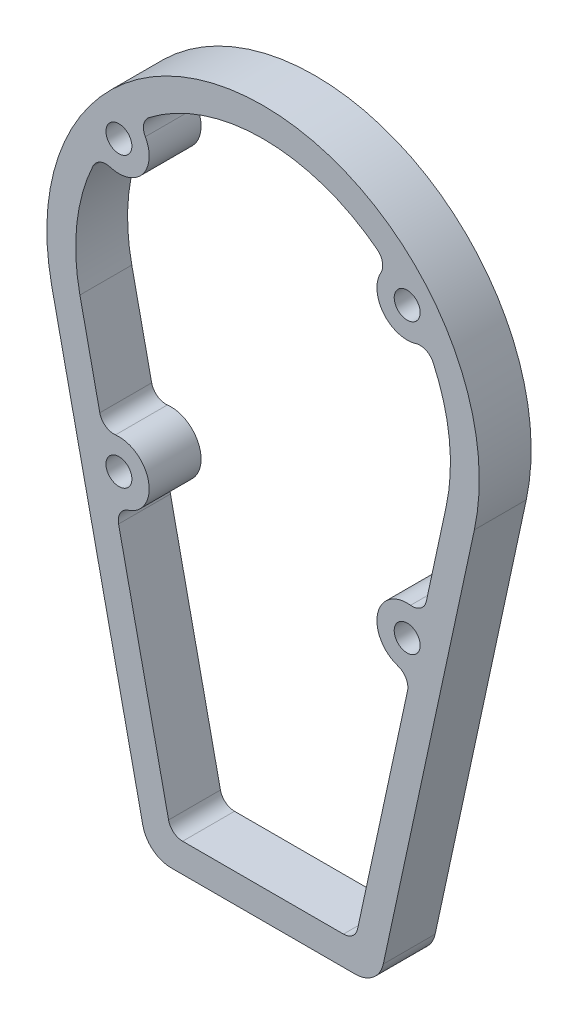
SolidWorks part; units mm, degrees
ref_plane "Front Plane" through (0, 0, 0) normal (0, 0, 1) x (1, 0, 0)
ref_plane "Top Plane" through (0, 0, 0) normal (0, 1, 0) x (1, 0, 0)
ref_plane "Right Plane" through (0, 0, 0) normal (1, 0, 0) x (0, 0, -1)
sketch "Sketch3" plane through (0, 0, 0) normal (0, 0, 1) x (1, 0, 0)
  line L0 (-31.9299, -122.5) -> (31.9299, -122.5)
  line L1 (41.7043, -114.6119) -> (73.3084, 31.6608)
  line L2 (-73.3084, 31.6608) -> (-41.7043, -114.6119)
  line L3 (-31.9299, -112.5) -> (-51.2845, -22.9211)
  line L4 (31.9299, -112.5) -> (51.2845, -22.9211)
  line L5 (-31.9299, -112.5) -> (31.9299, -112.5)
  line L6 (-55.4723, -3.5388) -> (-63.5339, 33.7727)
  line L8 (55.4723, -3.5388) -> (63.5339, 33.7727)
  arc A0 (31.9299, -122.5) -> (41.7043, -114.6119) centre (31.9299, -112.5) ccw
  arc A1 (73.3084, 31.6608) -> (-73.3084, 31.6608) centre (0, 47.5) ccw
  arc A2 (-41.7043, -114.6119) -> (-31.9299, -122.5) centre (-31.9299, -112.5) ccw
  circle A3 centre (50, -12.5) radius 4.5
  circle A4 centre (50, 87.5) radius 4.5
  circle A5 centre (-50, 87.5) radius 4.5
  circle A6 centre (-50, -12.5) radius 4.5
  arc A7 (63.5339, 33.7727) -> (56.6488, 79.3733) centre (0, 47.5) ccw
  arc A8 (-56.6488, 79.3733) -> (-43.531, 95.7706) centre (-50, 87.5) ccw
  arc A9 (43.531, 95.7706) -> (56.6488, 79.3733) centre (50, 87.5) ccw
  arc A10 (55.4723, -3.5388) -> (51.2845, -22.9211) centre (50, -12.5) ccw
  arc A11 (-51.2845, -22.9211) -> (-55.4723, -3.5388) centre (-50, -12.5) ccw
  arc A13 (43.531, 95.7706) -> (-43.531, 95.7706) centre (0, 47.5) ccw
  arc A15 (-56.6488, 79.3733) -> (-63.5339, 33.7727) centre (0, 47.5) ccw
  dimension "D1" = 10
  dimension "D2" = 6
  dimension "D3" = 10
  dimension "D4" = 10
  dimension "D5" = 10
  dimension "D6" = 6
  dimension "D7" = 6
  dimension "D8" = 6
extrude "Boss-Extrude1" add sketch "Sketch3" along normal blind 18
fillet "Fillet1" radius 5 2 edges at (31.9299, -112.5, 9) (-31.9299, -112.5, 9)
fillet "Fillet2" radius 5 8 edges at (-55.4723, -3.5388, 9) (55.4723, -3.5388, 9) (51.2845, -22.9211, 9) (-51.2845, -22.9211, 9) (56.6488, 79.3733, 9) (43.531, 95.7706, 9) (-43.531, 95.7706, 9) (-56.6488, 79.3733, 9)
